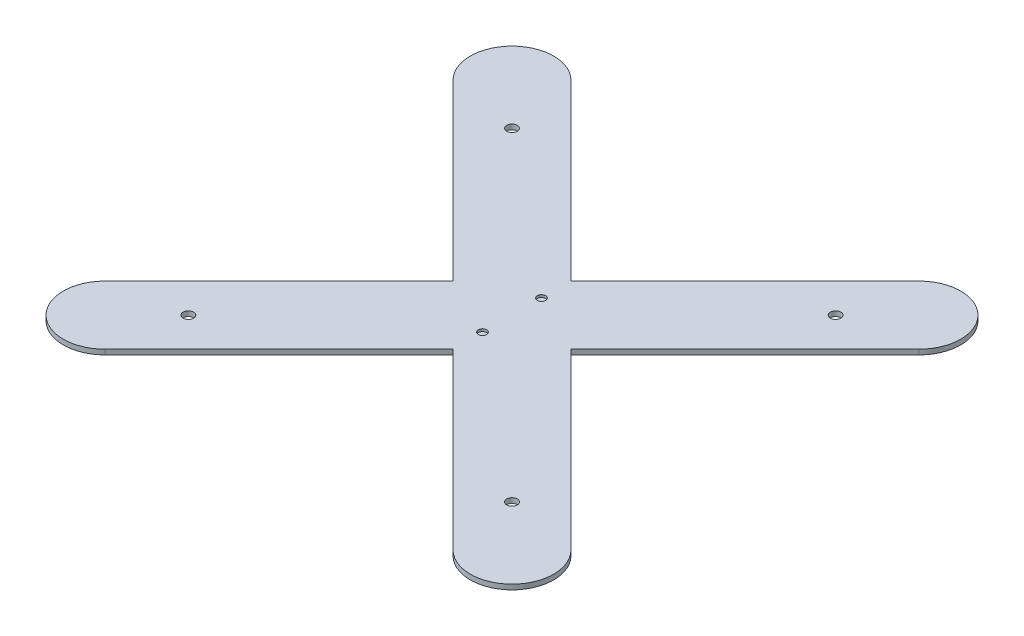
SolidWorks part; units mm, degrees
ref_plane "Front Plane" through (0, 0, 0) normal (0, 0, 1) x (1, 0, 0)
ref_plane "Top Plane" through (0, 0, 0) normal (0, 1, 0) x (1, 0, 0)
ref_plane "Right Plane" through (0, 0, 0) normal (1, 0, 0) x (0, 0, -1)
sketch "Sketch2" plane through (0, 0, 0) normal (0, 1, 0) x (1, 0, 0)
  line L0 (122, -122) -> (-122, 122) construction
  line L1 (-147, -147) -> (147, -147) construction
  line L2 (-147, -147) -> (-147, 147) construction
  line L3 (-147, 147) -> (147, 147) construction
  line L4 (147, -147) -> (147, 147) construction
  line L5 (-147, -147) -> (147, 147) construction
  line L6 (-147, 147) -> (147, -147) construction
  line L7 (104.3223, -139.6777) -> (0, -35.3553)
  line L8 (139.6777, -104.3223) -> (35.3553, 0)
  line L9 (-122, -122) -> (122, 122) construction
  line L10 (-139.6777, -104.3223) -> (-35.3553, 0)
  line L11 (-104.3223, -139.6777) -> (0, -35.3553)
  line L12 (0, 35.3553) -> (104.3223, 139.6777)
  line L13 (35.3553, 0) -> (139.6777, 104.3223)
  line L14 (-35.3553, 0) -> (-139.6777, 104.3223)
  line L15 (0, 35.3553) -> (-104.3223, 139.6777)
  line L16 (-147, 47) -> (-47, 147) construction
  line L17 (-147, 147) -> (-47, 147) construction
  line L18 (-147, 147) -> (-147, 47) construction
  line L19 (-147, 47) -> (-47, 47) construction
  line L20 (-47, 147) -> (-47, 47) construction
  line L21 (-147, 0) -> (147, 0) construction
  arc A0 (104.3223, -139.6777) -> (139.6777, -104.3223) centre (122, -122) ccw
  arc A1 (-104.3223, 139.6777) -> (-139.6777, 104.3223) centre (-122, 122) ccw
  arc A2 (-139.6777, -104.3223) -> (-104.3223, -139.6777) centre (-122, -122) ccw
  arc A3 (139.6777, 104.3223) -> (104.3223, 139.6777) centre (122, 122) ccw
  circle A5 centre (-97, 97) radius 3.15
  circle A6 centre (97, -97) radius 3.15
  circle A7 centre (97, 97) radius 3.15
  circle A8 centre (-97, -97) radius 3.15
  point P0 (0, 0)
  point P8 (0, 0)
  point P15 (0, 0)
extrude "Boss-Extrude2" add sketch "Sketch2" along normal blind 3
sketch "Sketch4" plane through (0, 3, 0) normal (0, 1, 0) x (1, 0, 0)
  line L0 (-35.3553, 0) -> (0, 0) construction
  line L1 (0, 0) -> (35.3553, 0) construction
  line L2 (0, 35.3553) -> (0, 0) construction
  circle A2 centre (0, 17.6777) radius 2.5
  circle A3 centre (0, -17.6777) radius 2.5
extrude "Cut-Extrude1" cut sketch "Sketch4" against normal blind 1.5
